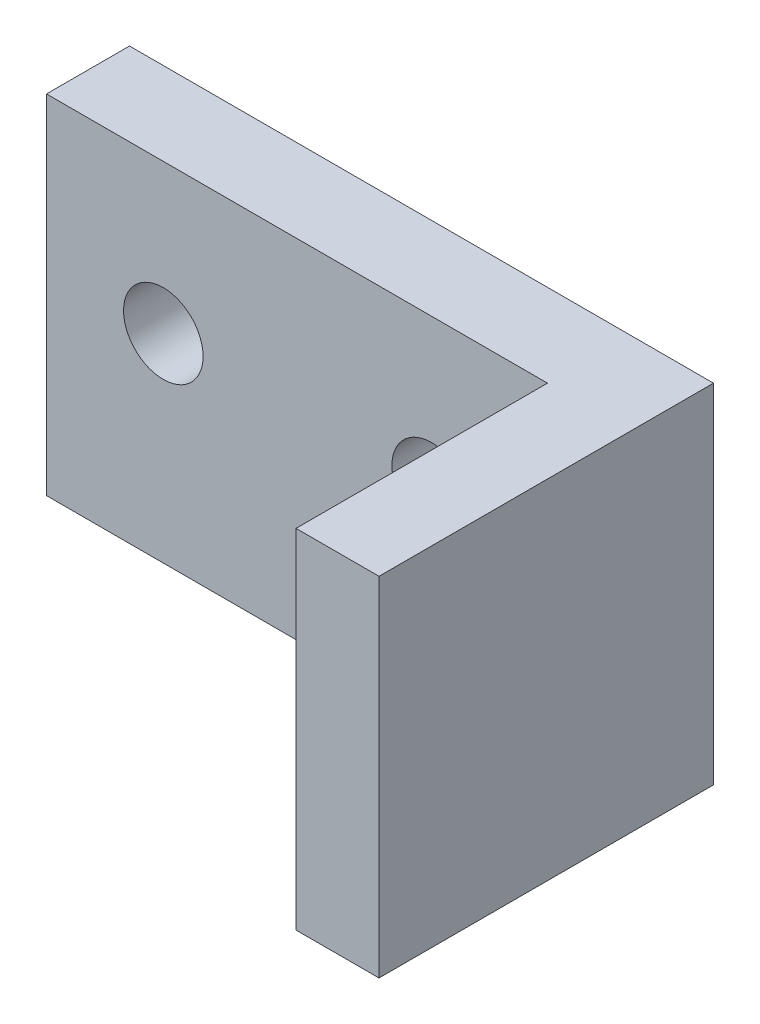
SolidWorks part; units mm, degrees
ref_plane "Ebene vorne" through (0, 0, 0) normal (0, 0, 1) x (1, 0, 0)
ref_plane "Ebene oben" through (0, 0, 0) normal (0, 1, 0) x (1, 0, 0)
ref_plane "Ebene rechts" through (0, 0, 0) normal (1, 0, 0) x (0, 0, -1)
sketch "Skizze1" plane through (0, 0, 0) normal (0, 1, 0) x (1, 0, 0)
  line L1 (-12.6, 12.65) -> (25.15, 12.65)
  line L2 (25.15, 12.65) -> (25.15, -12.65)
  line L3 (25.15, -12.65) -> (-12.6, -12.65)
  line L5 (-12.6, 10.85) -> (23.35, 10.85)
  line L6 (23.35, 10.85) -> (23.35, -10.85)
  line L7 (23.35, -10.85) -> (-12.6, -10.85)
  arc A0 (-12.6, 12.65) -> (-12.6, -12.65) centre (-12.6, 0) ccw
  arc A1 (-12.6, 10.85) -> (-12.6, -10.85) centre (-12.6, 0) ccw
sketch "Skizze2" plane through (0, 0, 0) normal (0, 0, 1) x (1, 0, 0)
  line L0 (0, 170) -> (0, 630)
sketch "Skizze3" plane through (0, 0, 0) normal (0, 0, 1) x (1, 0, 0)
  line L13 (-11, 155) -> (11, 155)
  line L15 (11, 155) -> (11, 130)
  line L17 (11, 130) -> (33.5, 130)
  line L18 (33.5, 130) -> (33.5, 205)
  line L19 (33.5, 205) -> (-33.5, 205)
  line L23 (-33.5, 130) -> (-33.5, 205)
  line L24 (-11, 130) -> (-33.5, 130)
  line L25 (-11, 155) -> (-11, 130)
  point P16 (0, 205)
  point P19 (0, 155)
sketch "Skizze4" plane through (0, 0, 0) normal (0, 1, 0) x (1, 0, 0)
  line L0 (25.15, -12.65) -> (33.5, -12.65)
  line L1 (33.5, -12.65) -> (33.5, 21)
  line L2 (33.5, 21) -> (-25.25, 21)
  line L3 (25.15, -12.65) -> (25.15, 12.65)
  line L4 (25.15, 12.65) -> (-25.25, 12.65)
  line L5 (-25.25, 12.65) -> (-25.25, 21)
extrude "Aufsatz-Linear austragen1" add sketch "Skizze4" along normal up to vertex (205 mm away) from vertex at 170 starting at point (0, 170, 0)
sketch "Holes" plane through (0, 0, 0) normal (0, 0, 1) x (1, 0, 0)
  circle A0 centre (13.5, 190) radius 4
  circle A1 centre (-13.5, 190) radius 4
sketch "Skizze6" plane through (0, 0, 0) normal (0, 0, 1) x (1, 0, 0)
  circle A0 centre (-13.5, 190) radius 4
  circle A1 centre (13.5, 190) radius 4
extrude "Schnitt-Linear austragen1" cut sketch "Skizze6" against normal up to surface (21 mm away) up to face at (4.125, 187.5, -21)
